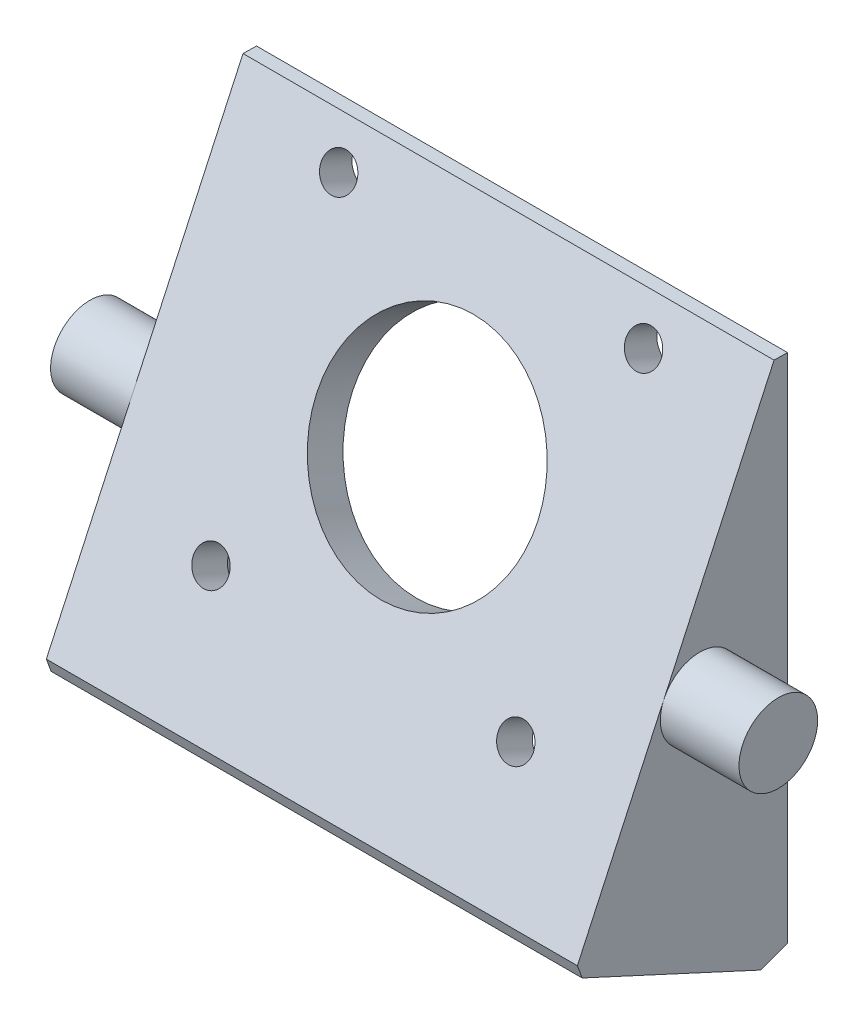
SolidWorks part; units mm, degrees
material "ABS"
ref_plane "Front" through (0, 0, 0) normal (0, 0, 1) x (1, 0, 0)
ref_plane "Top" through (0, 0, 0) normal (0, 1, 0) x (1, 0, 0)
ref_plane "Right" through (0, 0, 0) normal (1, 0, 0) x (0, 0, -1)
sketch "Croquis1" plane through (0, 0, 0) normal (1, 0, 0) x (0, 0, -1)
  line L0 (0, 28.6356) -> (0, -28.6356)
  line L1 (0, -28.6356) -> (-21.791, -18.5782)
  line L2 (-21.791, -18.5782) -> (0, 28.6356)
  dimension "D1" = 52
  dimension "D2" = 24
extrude "Saliente-Extruir1" add sketch "Croquis1" along normal mid plane 54
shell "Vaciado1" thickness 4
sketch "Croquis2" plane through (0, 3.3525, 7.2637) normal (0, -0.4191, -0.908) x (1, 0, 0)
  line L0 (23, 22) -> (-23, 22) construction
  line L5 (-15.5, 12.5) -> (15.5, 12.5) construction
  line L6 (-15.5, 12.5) -> (-15.5, -18.5) construction
  line L7 (-15.5, -18.5) -> (15.5, -18.5) construction
  line L8 (15.5, 12.5) -> (15.5, -18.5) construction
  line L9 (-15.5, 12.5) -> (15.5, -18.5) construction
  line L10 (-15.5, -18.5) -> (15.5, 12.5) construction
  circle A2 centre (0, -3) radius 11.25
  circle A3 centre (15.5, -18.5) radius 1.8
  circle A4 centre (-15.5, -18.5) radius 1.8
  circle A5 centre (-15.5, 12.5) radius 1.8
  circle A6 centre (15.5, 12.5) radius 1.8
  dimension "D1" = 22.5
  dimension "D3" = 3.6
  dimension "D2" = 25
  dimension "D4" = 31
  dimension "D5" = 31
extrude "NEMA" cut sketch "Croquis2" against normal up to next
sketch "Croquis4" plane through (0, 5.0287, 10.8955) normal (0, 0.4191, 0.908) x (1, 0, 0)
  line L0 (-15.5, 17) -> (-15.5, 20) construction
  line L1 (-17.3, 17) -> (-17.3, 20)
  line L2 (-13.7, 17) -> (-13.7, 20)
  line L3 (15.5, 17) -> (15.5, 20) construction
  line L4 (13.7, 17) -> (13.7, 20)
  line L5 (17.3, 17) -> (17.3, 20)
  line L6 (15.5, -14) -> (15.5, -11) construction
  line L7 (15.5, -12.5) -> (15.5, 18.5) construction
  line L8 (13.7, -14) -> (13.7, -11)
  line L9 (17.3, -14) -> (17.3, -11)
  line L10 (-15.5, -14) -> (-15.5, -11) construction
  line L11 (-15.5, -12.5) -> (-15.5, 18.5) construction
  line L12 (-17.3, -14) -> (-17.3, -11)
  line L13 (-13.7, -14) -> (-13.7, -11)
  line L14 (0, 1.5) -> (0, 4.5) construction
  line L15 (-11.25, 1.5) -> (-11.25, 4.5)
  line L16 (11.25, 1.5) -> (11.25, 4.5)
  arc A0 (-17.3, 17) -> (-13.7, 17) centre (-15.5, 17) ccw
  arc A1 (-13.7, 20) -> (-17.3, 20) centre (-15.5, 20) ccw
  circle A2 centre (-15.5, 18.5) radius 1.8 construction
  arc A3 (13.7, 17) -> (17.3, 17) centre (15.5, 17) ccw
  arc A4 (17.3, 20) -> (13.7, 20) centre (15.5, 20) ccw
  arc A5 (13.7, -14) -> (17.3, -14) centre (15.5, -14) ccw
  arc A6 (17.3, -11) -> (13.7, -11) centre (15.5, -11) ccw
  arc A7 (-17.3, -14) -> (-13.7, -14) centre (-15.5, -14) ccw
  arc A8 (-13.7, -11) -> (-17.3, -11) centre (-15.5, -11) ccw
  arc A9 (-11.25, 1.5) -> (11.25, 1.5) centre (0, 1.5) ccw
  arc A10 (11.25, 4.5) -> (-11.25, 4.5) centre (0, 4.5) ccw
  circle A11 centre (0, 3) radius 11.25 construction
  point P2 (-15.5, 18.5)
  point P12 (15.5, 18.5)
  point P19 (15.5, -12.5)
  point P29 (-15.5, -12.5)
  point P40 (0, 3)
  dimension "D1" = 3
extrude "NEMA-OVALES" [suppressed] cut sketch "Croquis4" against normal up to next
chamfer "Chaflán1" distance 1 angle 45 1 edges at (0, -18.5782, 21.791)
chamfer "Chaflán2" distance 3 angle 89 1 edges at (0, 28.6356, 0)
chamfer "Chaflán3" distance 3 angle 45 1 edges at (0, -28.6356, 0)
fillet "Redondeo1" radius 2 5 edges at (-23, -20.4264, 8.2415) (-23, 1.2339, 8.2415) (0, -16.6226, 16.483) (23, 1.2339, 8.2415) (23, -20.4264, 8.2415)
sketch "Croquis3" plane through (0, -19.9751, 9.2193) normal (0, 0.908, -0.4191) x (1, 0, 0)
  line L0 (-12, 9) -> (-12, -5) construction
  line L1 (-10.2, 9) -> (-10.2, -5)
  line L2 (-13.8, 9) -> (-13.8, -5)
  line L3 (0, 0) -> (0, -11.8087) construction
  line L5 (-12, 31) -> (-12, 17) construction
  line L6 (-10.2, 31) -> (-10.2, 17)
  line L7 (-13.8, 31) -> (-13.8, 17)
  line L8 (-12, 9) -> (-12, 31) construction
  line L9 (12, 9) -> (12, -5) construction
  line L10 (10.2, 9) -> (10.2, -5)
  line L11 (13.8, 9) -> (13.8, -5)
  line L12 (12, 31) -> (12, 17) construction
  line L13 (10.2, 31) -> (10.2, 17)
  line L14 (13.8, 31) -> (13.8, 17)
  line L15 (12, 9) -> (12, 31) construction
  line L16 (-27, -12) -> (27, -12) construction
  arc A0 (-10.2, 9) -> (-13.8, 9) centre (-12, 9) ccw
  arc A1 (-13.8, -5) -> (-10.2, -5) centre (-12, -5) ccw
  arc A2 (-10.2, 31) -> (-13.8, 31) centre (-12, 31) ccw
  arc A3 (-13.8, 17) -> (-10.2, 17) centre (-12, 17) ccw
  arc A4 (10.2, 9) -> (13.8, 9) centre (12, 9) cw
  arc A5 (13.8, -5) -> (10.2, -5) centre (12, -5) cw
  arc A6 (10.2, 31) -> (13.8, 31) centre (12, 31) cw
  arc A7 (13.8, 17) -> (10.2, 17) centre (12, 17) cw
  point P2 (-12, 2)
  point P10 (-12, -6.8)
  point P16 (-12, 24)
  point P24 (12, 2)
  point P31 (12, 24)
  dimension "D1" = 3.6
  dimension "D2" = 24
  dimension "D3" = 14
  dimension "D4" = 14
  dimension "D6" = 22
  dimension "D5" = 2
extrude "MONTAJE" [suppressed] cut sketch "Croquis3" against normal up to next
sketch "Croquis6" plane through (27, 0, 0) normal (1, 0, 0) x (0, 0, -1)
  line L0 (-1.3735, 25.6596) -> (-21.372, -17.6703) construction
  line L2 (-20.8831, -18.9973) -> (-2.7239, -27.3785) construction
  circle A0 centre (-8.9399, -0.2794) radius 4
  dimension "D1" = 8
  dimension "D2" = 22
extrude "EJE" add sketch "Croquis6" along normal blind 8
mirror "Simetría1" about plane through (0, 0, 0) normal (1, 0, 0) of "EJE"
